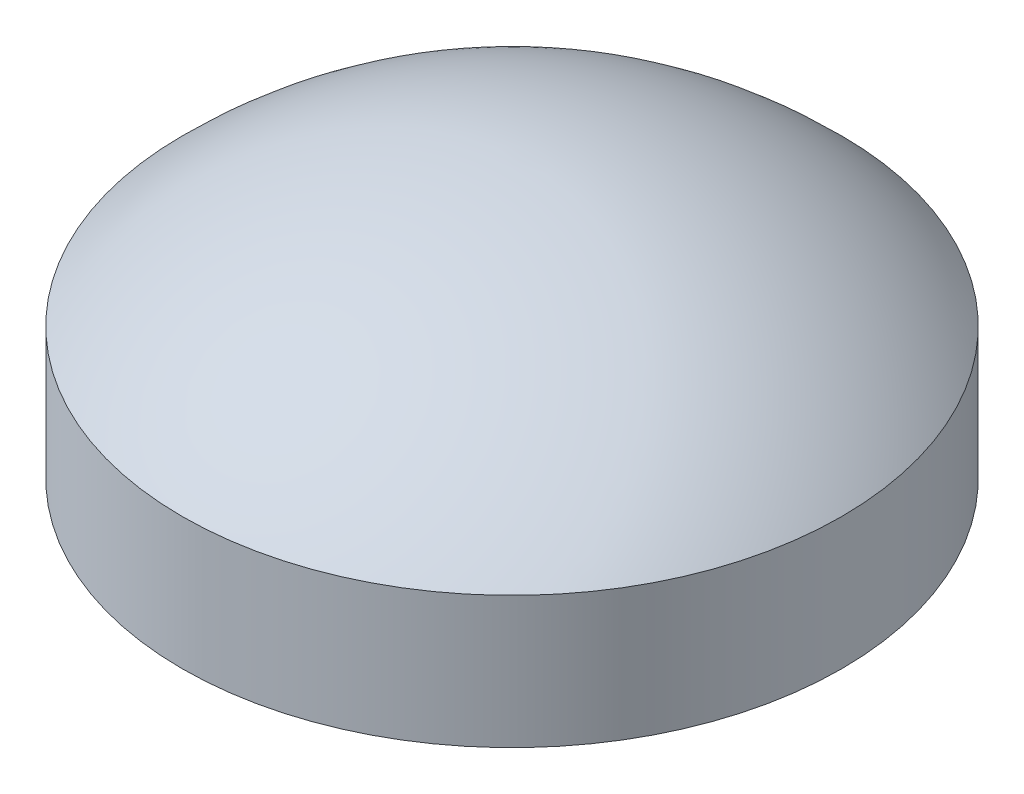
SolidWorks part; units mm, degrees
ref_plane "Front Plane" through (0, 0, 0) normal (0, 0, 1) x (1, 0, 0)
ref_plane "Top Plane" through (0, 0, 0) normal (0, 1, 0) x (1, 0, 0)
ref_plane "Right Plane" through (0, 0, 0) normal (1, 0, 0) x (0, 0, -1)
sketch "Sketch1" plane through (0, 0, 0) normal (0, 0, 1) x (1, 0, 0)
  line L0 (0, -0.436) -> (0, 14.1839) construction
  line L1 (-100, -42.0204) -> (-100, -82.0204)
  line L2 (-97, -43.2529) -> (-97, -82.0204)
  line L3 (-100, -82.0204) -> (-97, -82.0204)
  line L4 (0, 0) -> (0, -3)
  arc A1 (0, 0) -> (-100, -42.0204) centre (0, -140) ccw
  arc A2 (0, -3) -> (-97, -43.2529) centre (0, -140) ccw
  dimension "D2" = 0
  dimension "D1" = 140
  dimension "D4" = 40
  dimension "D5" = 0
  dimension "D3" = 100
  dimension "D6" = 3
revolve "Revolve1" add sketch "Sketch1" angle 360 about L4
